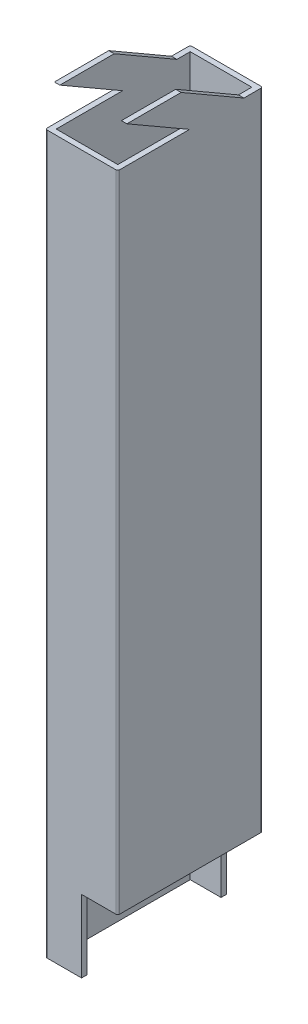
SolidWorks part; units mm, degrees
ref_plane "Front Plane" through (0, 0, 0) normal (0, 0, 1) x (1, 0, 0)
ref_plane "Top Plane" through (0, 0, 0) normal (0, 1, 0) x (1, 0, 0)
ref_plane "Right Plane" through (0, 0, 0) normal (1, 0, 0) x (0, 0, -1)
sketch "Sketch1" plane through (0, 0, 0) normal (0, 1, 0) x (1, 0, 0)
  line L0 (1.5, 1.5) -> (18.5, 1.5)
  line L1 (0.5, 0) -> (19.5, 0)
  line L2 (0, 0.5) -> (0, 39.5)
  line L3 (0.5, 40) -> (19.5, 40)
  line L4 (20, 0.5) -> (20, 39.5)
  line L5 (18.5, 1.5) -> (18.5, 38.5)
  line L6 (1.5, 38.5) -> (18.5, 38.5)
  line L7 (1.5, 1.5) -> (1.5, 38.5)
  arc A0 (19.5, 0) -> (20, 0.5) centre (19.5, 0.5) ccw
  arc A1 (0.5, 0) -> (0, 0.5) centre (0.5, 0.5) cw
  arc A2 (0, 39.5) -> (0.5, 40) centre (0.5, 39.5) cw
  arc A3 (19.5, 40) -> (20, 39.5) centre (19.5, 39.5) cw
  arc A4 (18.5, 1.5) -> (18.5, 1.5) centre (18.5, 1.5) ccw
  arc A5 (18.5, 38.5) -> (18.5, 38.5) centre (18.5, 38.5) cw
  arc A6 (1.5, 38.5) -> (1.5, 38.5) centre (1.5, 38.5) cw
  arc A7 (1.5, 1.5) -> (1.5, 1.5) centre (1.5, 1.5) cw
  point P9 (0, 0)
  dimension "D3" = 0.5
  dimension "D1" = 20
  dimension "D2" = 40
  dimension "D4" = 1.5
extrude "Boss-Extrude1" add sketch "Sketch1" along normal blind 208
sketch "Sketch2" plane through (0, 0, 0) normal (0, 0, 1) x (1, 0, 0)
  line L0 (10, 20) -> (10, 0)
  line L1 (20, 0) -> (10, 0)
  line L2 (20, 0) -> (20, 20)
  line L3 (20, 20) -> (10, 20)
  line L5 (0.5, 0) -> (19.5, 0) construction
  dimension "D1" = 20
extrude "Cut-Extrude1" cut sketch "Sketch2" against normal blind 40
sketch "Sketch3" plane through (0, 0, 0) normal (1, 0, 0) x (0, 0, -1)
  line L6 (0, 208) -> (0, 198)
  line L7 (0, 208) -> (0, 0) construction
  line L8 (0, 198) -> (19.8205, 198)
  line L9 (19.8205, 198) -> (2.5, 208)
  line L10 (39.5, 208) -> (0.5, 208) construction
  line L11 (2.5, 208) -> (0, 208)
  line L12 (17.5, 208) -> (34.8205, 198)
  line L13 (34.8205, 198) -> (40, 198)
  line L14 (40, 208) -> (40, 0) construction
  line L15 (40, 198) -> (40, 208)
  line L16 (40, 208) -> (17.5, 208)
  dimension "D1" = 15
  dimension "D2" = 10
  dimension "D3" = 30
  dimension "10" = 2.5
extrude "Cut-Extrude2" cut sketch "Sketch3" along normal blind 40
